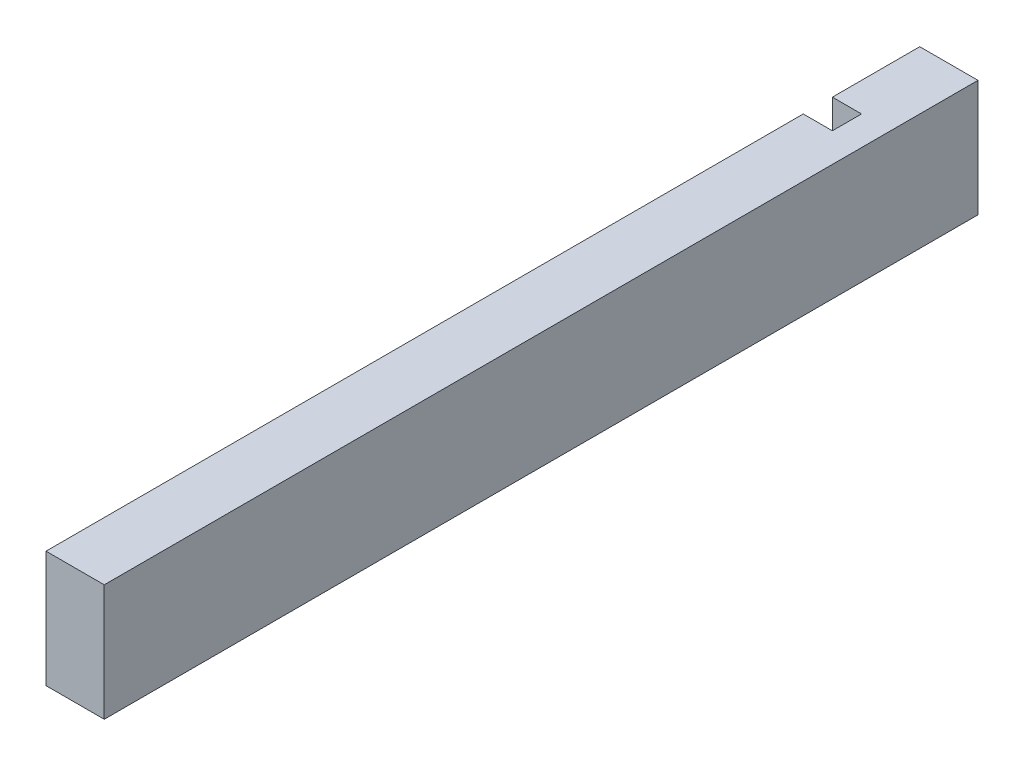
SolidWorks part; units mm, degrees
ref_plane "Plan de face" through (0, 0, 0) normal (0, 0, 1) x (1, 0, 0)
ref_plane "Plan de dessus" through (0, 0, 0) normal (0, 1, 0) x (1, 0, 0)
ref_plane "Plan de droite" through (0, 0, 0) normal (1, 0, 0) x (0, 0, -1)
sketch "Esquisse1" plane through (0, 0, 0) normal (0, 0, 1) x (1, 0, 0)
  line L1 (0, 0) -> (20, 0)
  line L2 (0, 0) -> (0, 40)
  line L3 (0, 40) -> (20, 40)
  line L4 (20, 0) -> (20, 40)
  dimension "D1" = 20
  dimension "D2" = 40
extrude "Boss.-Extru.1" add sketch "Esquisse1" along normal blind 300
sketch "Esquisse2" plane through (0, 0, 0) normal (0, -1, 0) x (1, 0, 0)
  line L0 (0, 0) -> (0, 30) construction
  line L1 (0, 300) -> (0, 0) construction
  line L2 (0, 30) -> (10, 30)
  line L3 (10, 30) -> (10, 40)
  line L4 (10, 40) -> (0, 40)
  dimension "D1" = 30
  dimension "D2" = 10
  dimension "D3" = 10
extrude "Enlèv. mat.-Extru.1" cut sketch "Esquisse2" against normal through all and the other way through all
